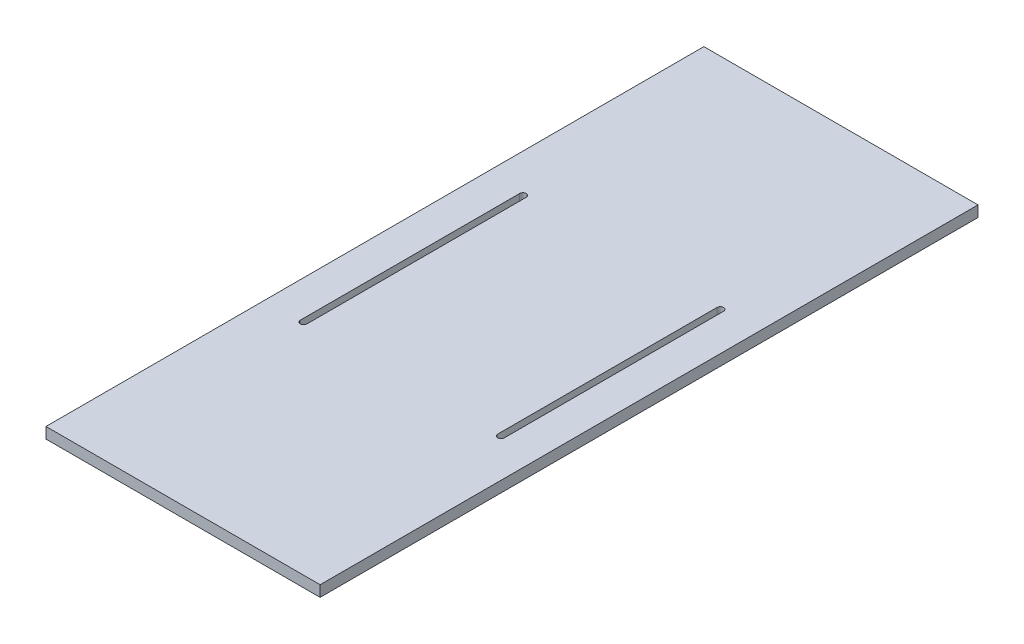
SolidWorks part; units mm, degrees
ref_plane "前视基准面" through (0, 0, 0) normal (0, 0, 1) x (1, 0, 0)
ref_plane "上视基准面" through (0, 0, 0) normal (0, 1, 0) x (1, 0, 0)
ref_plane "右视基准面" through (0, 0, 0) normal (1, 0, 0) x (0, 0, -1)
sketch "草图1" plane through (0, 0, 0) normal (0, 1, 0) x (1, 0, 0)
  line L1 (125, -300) -> (-125, -300)
  line L2 (125, -300) -> (125, 300)
  line L3 (125, 300) -> (-125, 300)
  line L4 (-125, -300) -> (-125, 300)
  line L5 (125, -300) -> (-125, 300) construction
  line L6 (125, 300) -> (-125, -300) construction
  point P0 (0, 0)
  dimension "D1" = 250
  dimension "D2" = 600
extrude "凸台-拉伸1" add sketch "草图1" along normal mid plane 10
sketch "草图2" plane through (0, 5, 0) normal (0, 1, 0) x (1, 0, 0)
  line L0 (-90, 300) -> (-90, -300) construction
  line L1 (125, 300) -> (-125, 300) construction
  line L2 (-125, -300) -> (125, -300) construction
  line L3 (0, 300) -> (0, -300) construction
  line L4 (90, 300) -> (90, -300) construction
  line L5 (-90, 100) -> (-90, -100) construction
  line L6 (-87, 100) -> (-87, -100)
  line L7 (-93, 100) -> (-93, -100)
  line L8 (90, 100) -> (90, -100) construction
  line L9 (87, 100) -> (87, -100)
  line L10 (93, 100) -> (93, -100)
  arc A0 (-87, 100) -> (-93, 100) centre (-90, 100) ccw
  arc A1 (-93, -100) -> (-87, -100) centre (-90, -100) ccw
  arc A2 (87, 100) -> (93, 100) centre (90, 100) cw
  arc A3 (93, -100) -> (87, -100) centre (90, -100) cw
  point P12 (-90, 0)
  point P17 (0, 0)
  point P20 (90, 0)
  dimension "D3" = 3
  dimension "D1" = 180
  dimension "D2" = 200
extrude "切除-拉伸1" cut sketch "草图2" against normal through all
